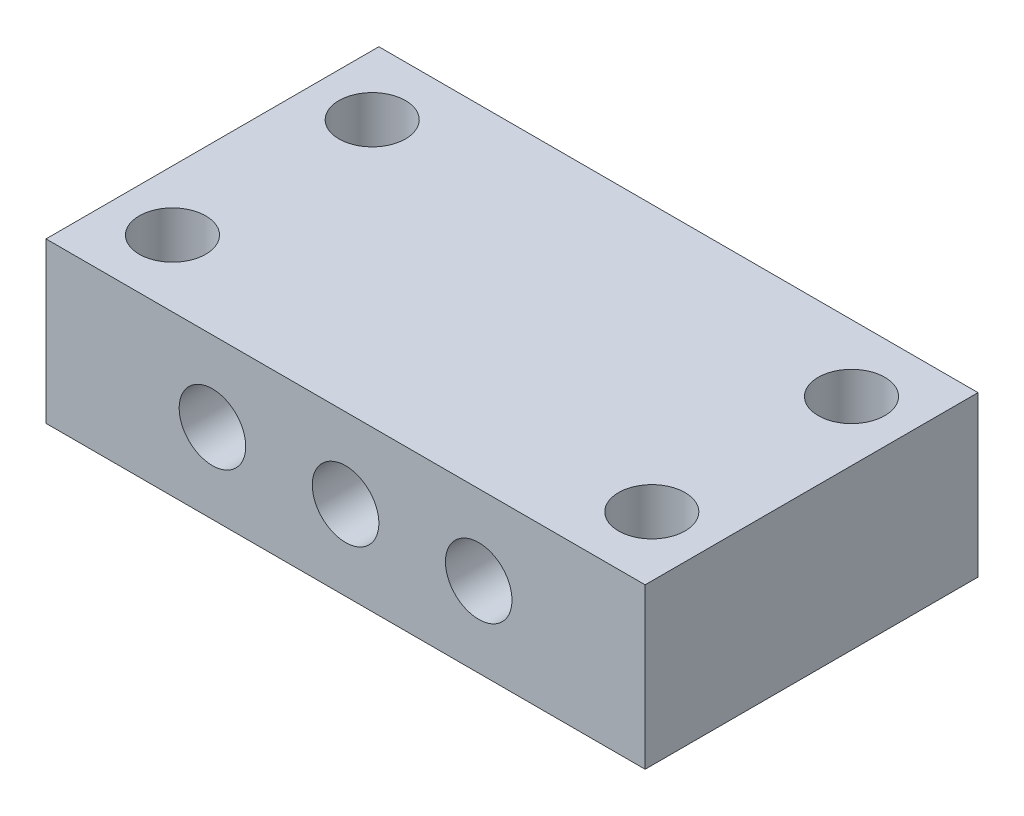
SolidWorks part; units mm, degrees
ref_plane "Front Plane" through (0, 0, 0) normal (0, 0, 1) x (1, 0, 0)
ref_plane "Top Plane" through (0, 0, 0) normal (0, 1, 0) x (1, 0, 0)
ref_plane "Right Plane" through (0, 0, 0) normal (1, 0, 0) x (0, 0, -1)
sketch "Sketch1" plane through (0, 0, 0) normal (0, 1, 0) x (1, 0, 0)
  line L1 (-22.5, 12.5) -> (22.5, 12.5)
  line L2 (-22.5, 12.5) -> (-22.5, -12.5)
  line L3 (-22.5, -12.5) -> (22.5, -12.5)
  line L4 (22.5, 12.5) -> (22.5, -12.5)
  line L5 (-22.5, 12.5) -> (22.5, -12.5) construction
  line L6 (-22.5, -12.5) -> (22.5, 12.5) construction
  point P0 (0, 0)
  dimension "D1" = 25
  dimension "D2" = 45
extrude "Boss-Extrude1" add sketch "Sketch1" along normal blind 12
sketch "Sketch2" plane through (0, 12, 0) normal (0, 1, 0) x (1, 0, 0)
  line L0 (-22.5, -12.5) -> (22.5, -12.5) construction
  line L1 (22.5, 12.5) -> (-22.5, 12.5) construction
  line L2 (-22.5, 12.5) -> (-22.5, -12.5) construction
  line L3 (22.5, -12.5) -> (22.5, 12.5) construction
  circle A0 centre (-18, -7.5) radius 2.5
  circle A1 centre (-18, 7.5) radius 2.5
  circle A2 centre (18, -7.5) radius 2.5
  circle A3 centre (18, 7.5) radius 2.5
  dimension "D1" = 5
  dimension "D2" = 5
  dimension "D3" = 5
  dimension "D4" = 5
  dimension "D5" = 4.5
  dimension "D6" = 4.5
  dimension "D7" = 4.5
  dimension "D8" = 4.5
extrude "Cut-Extrude1" cut sketch "Sketch2" against normal blind 12
sketch "Sketch3" plane through (0, 0, -12.5) normal (0, 0, -1) x (-1, 0, 0)
  circle A0 centre (0, 6) radius 2.5
extrude "Cut-Extrude2" cut sketch "Sketch3" against normal blind 72
sketch "Sketch4" plane through (0, 0, -12.5) normal (0, 0, -1) x (-1, 0, 0)
  line L0 (-22.5, 12) -> (22.5, 12) construction
  circle A0 centre (10, 6) radius 2.5
  circle A1 centre (-10, 6) radius 2.5
  circle A2 centre (0, 6) radius 2.5 construction
  point P6 (0, 12)
  dimension "D1" = 10
  dimension "D2" = 10
extrude "Cut-Extrude3" cut sketch "Sketch4" against normal blind 72
